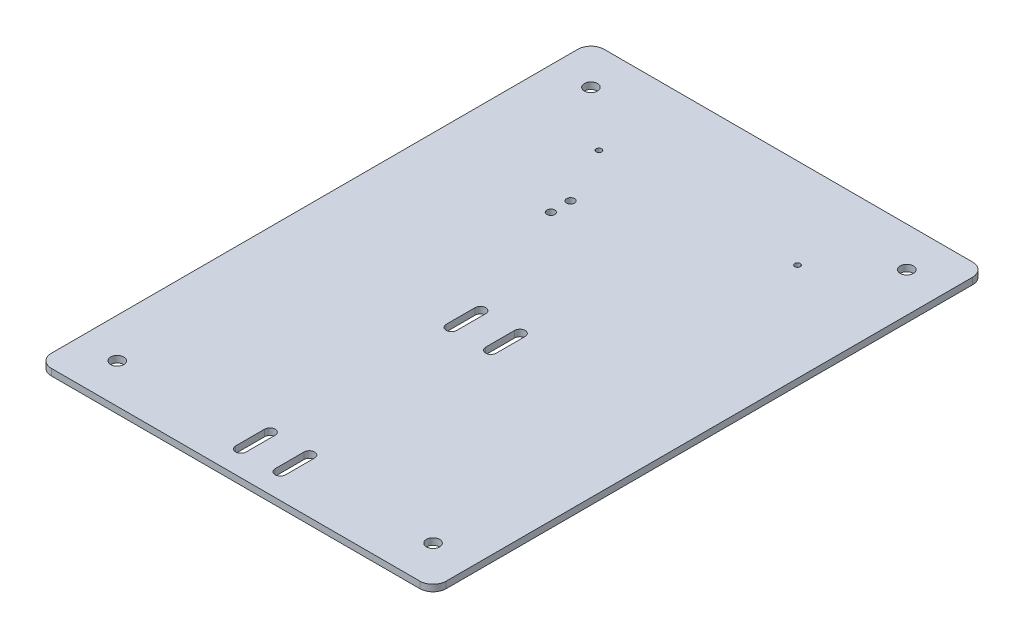
SolidWorks part; units mm, degrees
ref_plane "Ebene vorne" through (0, 0, 0) normal (0, 0, 1) x (1, 0, 0)
ref_plane "Ebene oben" through (0, 0, 0) normal (0, 1, 0) x (1, 0, 0)
ref_plane "Ebene rechts" through (0, 0, 0) normal (1, 0, 0) x (0, 0, -1)
sketch "Side" plane through (0, 0, 0) normal (0, 0, 1) x (1, 0, 0)
  line L1 (-150, -16) -> (150, -16)
  line L2 (-150, -16) -> (-150, -21)
  line L3 (-150, -21) -> (150, -21)
  line L4 (150, -16) -> (150, -21)
sketch "Skizze2" plane through (0, 0, 0) normal (0, 0, 1) x (1, 0, 0)
  line L1 (-150, -16) -> (150, -16)
  line L2 (-150, -16) -> (-150, -21)
  line L3 (-150, -21) -> (150, -21)
  line L4 (150, -16) -> (150, -21)
extrude "Aufsatz-Linear austragen1" add sketch "Skizze2" against normal blind 120 and the other way blind 300
sketch "Skizze3" plane through (0, 0, 0) normal (0, 1, 0) x (1, 0, 0)
  line L0 (0, -95) -> (0, -285) construction
  line L1 (55, -285) -> (55, -95)
  line L2 (55, -285) -> (-55, -285)
  line L3 (-55, -285) -> (-55, -95)
  line L4 (55, -95) -> (-55, -95)
  line L5 (55, -285) -> (-55, -95) construction
  line L6 (-55, -285) -> (55, -95) construction
  line L16 (0, -190) -> (0, -150.9424) construction
  line L27 (-30, -285) -> (-30, -255)
  line L28 (-30, -285) -> (30, -285)
  line L29 (30, -285) -> (30, -255)
  line L30 (-30, -255) -> (30, -255)
  line L31 (0, -255) -> (-30, -255)
  line L32 (30, -255) -> (-30, -255)
  line L34 (30, -285) -> (-30, -285)
  line L35 (0, -190) -> (89.9295, -190) construction
  line L36 (30, -95) -> (-30, -95)
  line L39 (0, -125) -> (-30, -125)
  line L40 (-30, -125) -> (30, -125)
  line L41 (30, -95) -> (30, -125)
  line L42 (-30, -95) -> (30, -95)
  line L43 (-30, -95) -> (-30, -125)
  circle A0 centre (-15, -270) radius 3
  circle A1 centre (15, -270) radius 3
  circle A4 centre (15, -270) radius 3
  circle A5 centre (-15, -270) radius 3
  circle A6 centre (-15, -110) radius 3
  circle A7 centre (15, -110) radius 3
  circle A8 centre (15, -110) radius 3
  circle A9 centre (-15, -110) radius 3
  point P33 (0, -190)
sketch "Skizze4" plane through (0, -16, 0) normal (0, 1, 0) x (1, 0, 0)
  line L0 (-15, -121) -> (-15, -99) construction
  line L1 (-19, -121) -> (-19, -99)
  line L2 (-11, -121) -> (-11, -99)
  line L3 (0, -190) -> (0, -59.3409) construction
  line L4 (15, -121) -> (15, -99) construction
  line L5 (19, -121) -> (19, -99)
  line L6 (11, -121) -> (11, -99)
  line L7 (0, -190) -> (92.5411, -190) construction
  line L8 (-15, -259) -> (-15, -281) construction
  line L9 (-19, -259) -> (-19, -281)
  line L10 (-11, -259) -> (-11, -281)
  line L11 (15, -259) -> (15, -281) construction
  line L12 (19, -259) -> (19, -281)
  line L13 (11, -259) -> (11, -281)
  arc A0 (-19, -121) -> (-11, -121) centre (-15, -121) ccw
  arc A1 (-11, -99) -> (-19, -99) centre (-15, -99) ccw
  arc A2 (19, -121) -> (11, -121) centre (15, -121) cw
  arc A3 (11, -99) -> (19, -99) centre (15, -99) cw
  arc A4 (-19, -259) -> (-11, -259) centre (-15, -259) cw
  arc A5 (-11, -281) -> (-19, -281) centre (-15, -281) cw
  arc A6 (19, -259) -> (11, -259) centre (15, -259) ccw
  arc A7 (11, -281) -> (19, -281) centre (15, -281) ccw
  point P2 (-15, -110)
  point P8 (-15, -95)
  point P9 (-15, -125)
  point P16 (15, -110)
  point P24 (-15, -270)
  point P31 (15, -270)
  dimension "D1" = 30
  dimension "D2" = 4
extrude "Schnitt-Linear austragen1" cut sketch "Skizze4" against normal up to surface (5 mm away) up to face at (0, -21, 90)
sketch "Skizze5" plane through (0, 0, 0) normal (0, 1, 0) x (1, 0, 0)
  line L1 (0, 0) -> (30.9843, 0) construction
  line L4 (-65, -15) -> (65, -15)
  line L5 (-65, -15) -> (-65, 15)
  line L6 (-65, 15) -> (65, 15)
  line L7 (65, -15) -> (65, 15)
  line L8 (-65, -15) -> (65, 15) construction
  line L9 (-65, 15) -> (65, -15) construction
  circle A0 centre (53, -7.5) radius 1.65
  circle A1 centre (53, 7.5) radius 1.65
  circle A2 centre (-53, 7.5) radius 1.65
  circle A3 centre (-53, -7.5) radius 1.65
  point P8 (0, 0)
sketch "Skizze6" plane through (0, -16, 0) normal (0, 1, 0) x (1, 0, 0)
  circle A2 centre (-53, 7.5) radius 3
  circle A3 centre (-53, -7.5) radius 3
extrude "Schnitt-Linear austragen2" cut sketch "Skizze6" against normal up to surface (5 mm away) up to face at (15, -21, 110)
sketch "Skizze7" plane through (0, 0, 0) normal (0, 1, 0) x (1, 0, 0)
  circle A0 centre (-120, 90) radius 5
  circle A1 centre (120, 90) radius 5
  circle A2 centre (-120, -270) radius 5
  circle A3 centre (120, -270) radius 5
sketch "Skizze8" plane through (0, 0, 0) normal (0, 1, 0) x (1, 0, 0)
  circle A0 centre (-120, 90) radius 5
  circle A1 centre (120, 90) radius 5
  circle A2 centre (120, -270) radius 5
  circle A3 centre (-120, -270) radius 5
extrude "Schnitt-Linear austragen3" cut sketch "Skizze8" against normal up to surface (21 mm away) up to face at (-53, -21, -4.5)
fillet "Verrundung1" radius 10 4 edges at (-150, -18.5, -120) (150, -18.5, -120) (150, -18.5, 300) (-150, -18.5, 300)
sketch "Skizze9" plane through (0, -16, 0) normal (0, 1, 0) x (1, 0, 0)
  circle A0 centre (75.5, 51.5) radius 2.1
  circle A1 centre (-75.5, 51.5) radius 2.1
extrude "Schnitt-Linear austragen4" cut sketch "Skizze9" against normal up to surface (5 mm away) up to face at (-120, -21, 275)
